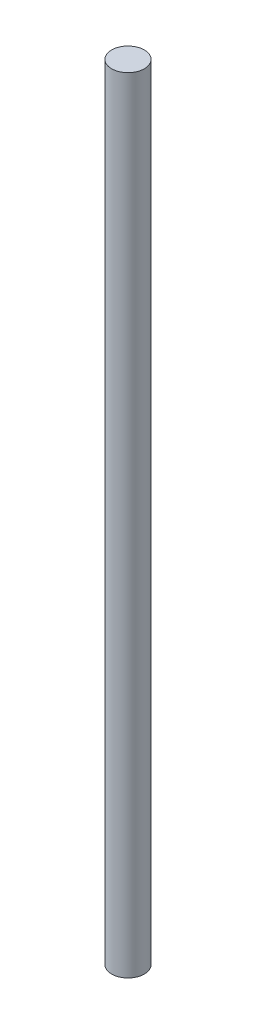
SolidWorks part; units mm, degrees
material "6061-T6 (SS)"
ref_plane "Front Plane" through (0, 0, 0) normal (0, 0, 1) x (1, 0, 0)
ref_plane "Top Plane" through (0, 0, 0) normal (0, 1, 0) x (1, 0, 0)
ref_plane "Right Plane" through (0, 0, 0) normal (1, 0, 0) x (0, 0, -1)
sketch "Sketch1" plane through (0, 0, 0) normal (0, 1, 0) x (1, 0, 0)
  circle A0 centre (0, 0) radius 6.35
  dimension "D1" = 12.7
extrude "Boss-Extrude1" add sketch "Sketch1" along normal blind 304.8
